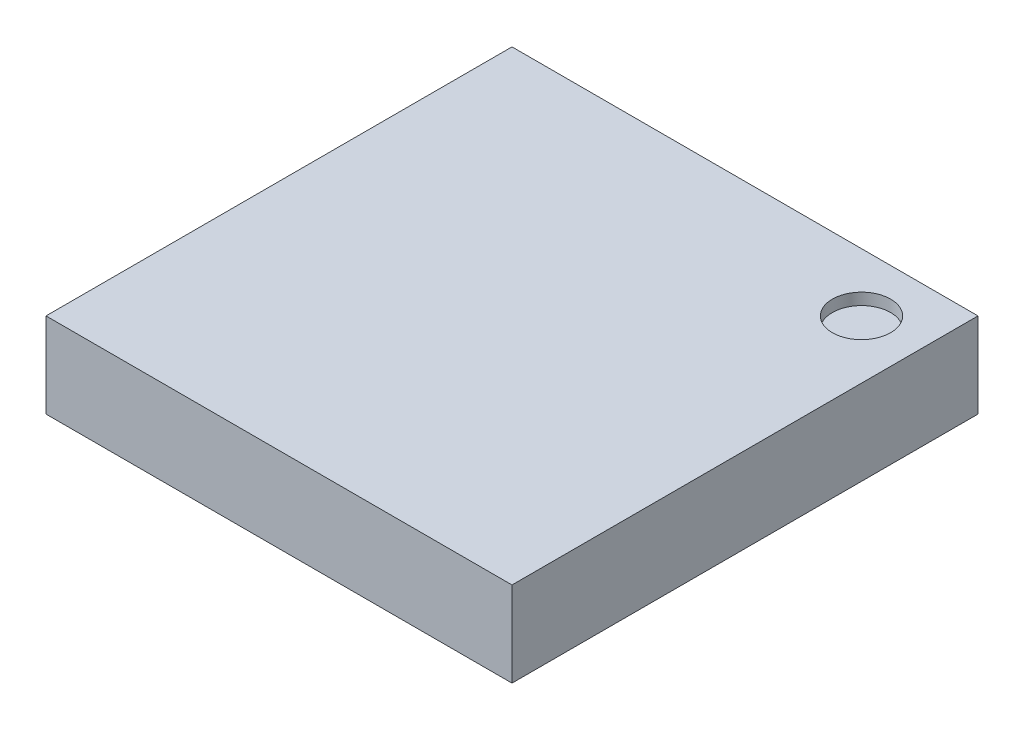
SolidWorks part; units mm, degrees
ref_plane "Front Plane" through (0, 0, 0) normal (0, 0, 1) x (1, 0, 0)
ref_plane "Top Plane" through (0, 0, 0) normal (0, 1, 0) x (1, 0, 0)
ref_plane "Right Plane" through (0, 0, 0) normal (1, 0, 0) x (0, 0, -1)
sketch "Sketch1" plane through (0, 0, 0) normal (0, 1, 0) x (1, 0, 0)
  line L1 (-2, -2) -> (2, -2)
  line L2 (-2, -2) -> (-2, 2)
  line L3 (-2, 2) -> (2, 2)
  line L4 (2, -2) -> (2, 2)
  line L5 (-2, -2) -> (2, 2) construction
  line L6 (-2, 2) -> (2, -2) construction
  point P0 (0, 0)
  dimension "D1" = 4
extrude "Boss-Extrude1" add sketch "Sketch1" along normal blind 0.73
sketch "Sketch2" plane through (0, 0.73, 0) normal (0, 1, 0) x (1, 0, 0)
  line L0 (2, 2) -> (-2, 2) construction
  line L1 (2, -2) -> (2, 2) construction
  circle A0 centre (1.5, 1.5) radius 0.25
  dimension "D3" = 0.5
  dimension "D1" = 0.5
  dimension "D2" = 0.5
extrude "Cut-Extrude1" cut sketch "Sketch2" against normal blind 0.1
